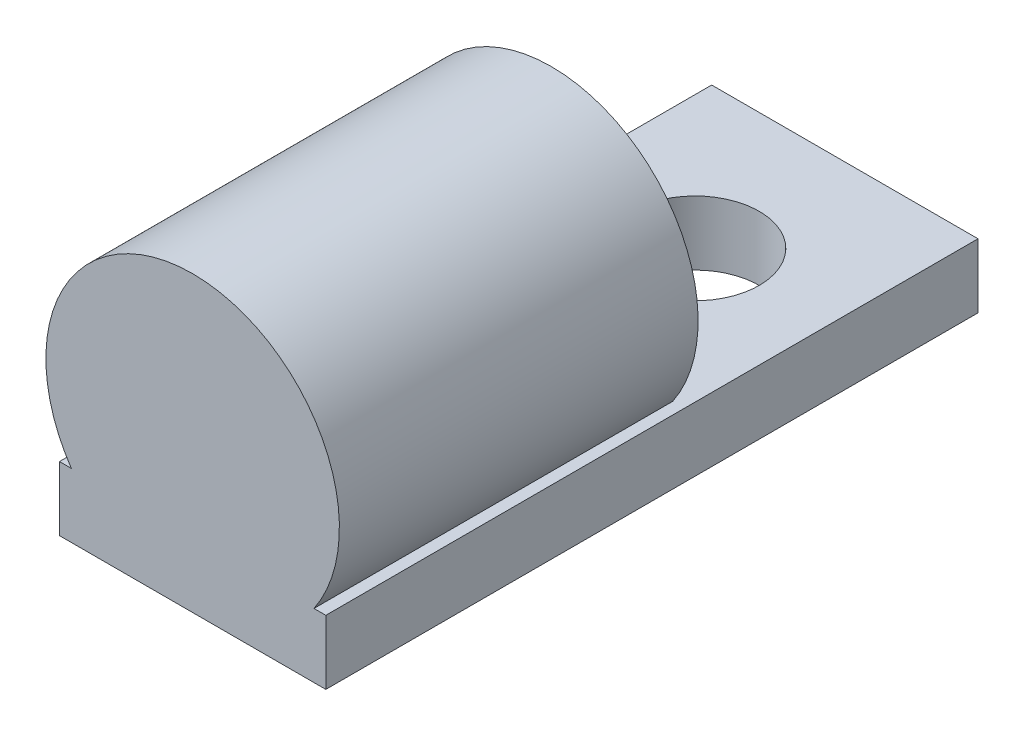
SolidWorks part; units mm, degrees
ref_plane "Front Plane" through (0, 0, 0) normal (0, 0, 1) x (1, 0, 0)
ref_plane "Top Plane" through (0, 0, 0) normal (0, 1, 0) x (1, 0, 0)
ref_plane "Right Plane" through (0, 0, 0) normal (1, 0, 0) x (0, 0, -1)
sketch "Sketch1" plane through (0, 0, 0) normal (0, 1, 0) x (1, 0, 0)
  line L1 (-6.223, 15.24) -> (6.223, 15.24)
  line L2 (-6.223, 15.24) -> (-6.223, -15.24)
  line L3 (-6.223, -15.24) -> (6.223, -15.24)
  line L4 (6.223, 15.24) -> (6.223, -15.24)
  line L5 (-6.223, 15.24) -> (6.223, -15.24) construction
  line L6 (-6.223, -15.24) -> (6.223, 15.24) construction
  circle A0 centre (0, 8.24) radius 3
  point P0 (0, 0)
  dimension "D2" = 6
  dimension "D1" = 12.446
  dimension "D3" = 7
  dimension "D4" = 30.48
extrude "Boss-Extrude1" add sketch "Sketch1" along normal blind 3
sketch "Sketch2" plane through (0, 0, 15.24) normal (0, 0, 1) x (1, 0, 0)
  line L0 (-6.223, 0) -> (6.223, 0) construction
  circle A0 centre (0, 6.858) radius 6.858
  dimension "D1" = 13.716
extrude "Boss-Extrude2" add sketch "Sketch2" against normal blind 16.764
